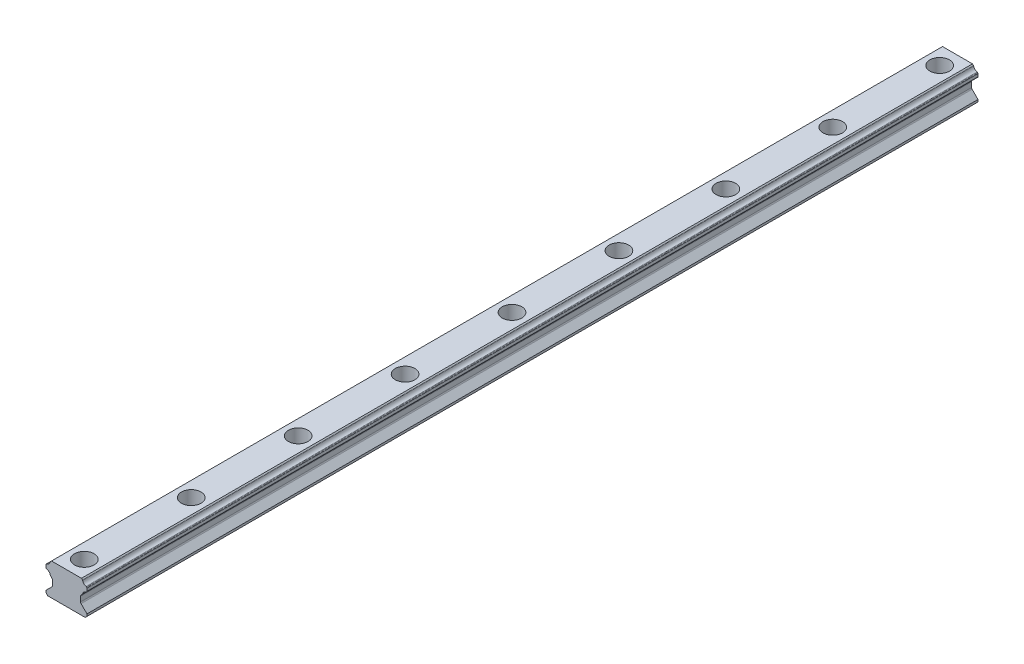
SolidWorks part; units mm, degrees
material "Plain Carbon Steel"
ref_plane "Front Plane" through (0, 0, 0) normal (0, 0, 1) x (1, 0, 0)
ref_plane "Top Plane" through (0, 0, 0) normal (0, 1, 0) x (1, 0, 0)
ref_plane "Right Plane" through (0, 0, 0) normal (1, 0, 0) x (0, 0, -1)
sketch "Sketch1" plane through (0, 0, 0) normal (0, 0, 1) x (1, 0, 0)
  line L0 (-8.1929, -12.4528) -> (-11.5, -15.7599)
  line L1 (-11.5, -17) -> (-10.5, -18)
  line L2 (0, 0) -> (0, -18) construction
  line L3 (-11.5, -15.7599) -> (-11.5, -17)
  line L4 (-10.5, -18) -> (10.5, -18)
  line L5 (11.5, -17) -> (11.5, -15.7599)
  line L6 (11.5, -15.7599) -> (8.1929, -12.4528)
  line L7 (10.5, -18) -> (11.5, -17)
  line L71 (-7.9, -11.7457) -> (-7.9, -8.9341)
  line L72 (-8.1929, -8.227) -> (-8.9352, -7.4847)
  line L73 (-11.1891, -5.2308) -> (-11.3536, -5.0663)
  line L74 (-11.5, -4.7128) -> (-11.5, -3.2984)
  line L75 (-11.3536, -2.9449) -> (-11.1751, -2.7664)
  line L76 (-8.9382, -0.5295) -> (-8.4087, 0)
  line L77 (-8.4087, 0) -> (8.4087, 0)
  line L78 (8.4087, 0) -> (8.9382, -0.5295)
  line L79 (11.1751, -2.7664) -> (11.3536, -2.9449)
  line L80 (11.5, -3.2984) -> (11.5, -4.7128)
  line L81 (11.3536, -5.0663) -> (11.1891, -5.2308)
  line L82 (8.9352, -7.4847) -> (8.1929, -8.227)
  line L83 (7.9, -8.9341) -> (7.9, -11.7457)
  arc A40 (-8.1929, -12.4528) -> (-7.9, -11.7457) centre (-8.9, -11.7457) ccw
  arc A41 (-7.9, -8.9341) -> (-8.1929, -8.227) centre (-8.9, -8.9341) ccw
  arc A42 (-9.0706, -7.2355) -> (-8.9352, -7.4847) centre (-8.5816, -7.1312) ccw
  arc A43 (-9.0706, -7.2355) -> (-10.9399, -5.3662) centre (-11.4471, -7.7427) ccw
  arc A44 (-11.1891, -5.2308) -> (-10.9399, -5.3662) centre (-10.8355, -4.8773) ccw
  arc A45 (-11.5, -4.7128) -> (-11.3536, -5.0663) centre (-11, -4.7128) ccw
  arc A46 (-11.3536, -2.9449) -> (-11.5, -3.2984) centre (-11, -3.2984) ccw
  arc A47 (-10.9283, -2.6315) -> (-11.1751, -2.7664) centre (-10.8216, -3.12) ccw
  arc A48 (-10.9283, -2.6315) -> (-9.0731, -0.7763) centre (-11.4471, -0.2575) ccw
  arc A49 (-8.9382, -0.5295) -> (-9.0731, -0.7763) centre (-8.5846, -0.883) ccw
  arc A50 (9.0731, -0.7763) -> (8.9382, -0.5295) centre (8.5846, -0.883) ccw
  arc A51 (9.0731, -0.7763) -> (10.9283, -2.6315) centre (11.4471, -0.2575) ccw
  arc A52 (11.1751, -2.7664) -> (10.9283, -2.6315) centre (10.8216, -3.12) ccw
  arc A53 (11.5, -3.2984) -> (11.3536, -2.9449) centre (11, -3.2984) ccw
  arc A54 (11.3536, -5.0663) -> (11.5, -4.7128) centre (11, -4.7128) ccw
  arc A55 (10.9399, -5.3662) -> (11.1891, -5.2308) centre (10.8355, -4.8773) ccw
  arc A56 (10.9399, -5.3662) -> (9.0706, -7.2355) centre (11.4471, -7.7427) ccw
  arc A57 (8.9352, -7.4847) -> (9.0706, -7.2355) centre (8.5816, -7.1312) ccw
  arc A58 (8.1929, -8.227) -> (7.9, -8.9341) centre (8.9, -8.9341) ccw
  arc A59 (7.9, -11.7457) -> (8.1929, -12.4528) centre (8.9, -11.7457) ccw
  point P30 (11.5, -18)
  point P40 (-11.5, -18)
  dimension "D3" = 18
  dimension "D4" = 45
  dimension "D5" = 23
extrude "Boss-Extrude1" add sketch "Sketch1" along normal blind 500
hole_wizard "CBORE for M6 Hex Socket Head Cap Screw1" positions "3DSketch1" profile "Sketch4" counterbore size "M6" standard "ISO" end condition through all
sketch3d "3DSketch1"
  line L0 (8.4087, 0, 0) -> (-8.4087, 0, 0) construction
  point P0 (0, 0, 10)
  dimension "D1" = 10
sketch "Sketch4" plane through (0, 0, 10) normal (1, 0, 0) x (0, 0, 1)
  line L0 (0, 0) -> (0, 18)
  line L1 (0, 18) -> (3.5, 18)
  line L3 (3.5, 18) -> (3.5, 9)
  line L4 (3.5, 9) -> (5.5, 9)
  line L5 (5.5, 9) -> (5.5, 0)
  line L7 (5.5, 0) -> (0, 0)
  line L11 (0, -6.35) -> (0, 107.95) construction
  dimension "Thru Hole Dia." = 7
  dimension "Thru Hole Depth" = 18
  dimension "C'Bore Dia." = 11
  dimension "C'Bore Depth" = 9
pattern_linear "LPattern1" count 9 spacing 60 along (0, 0, 1) of "CBORE for M6 Hex Socket Head Cap Screw1"
